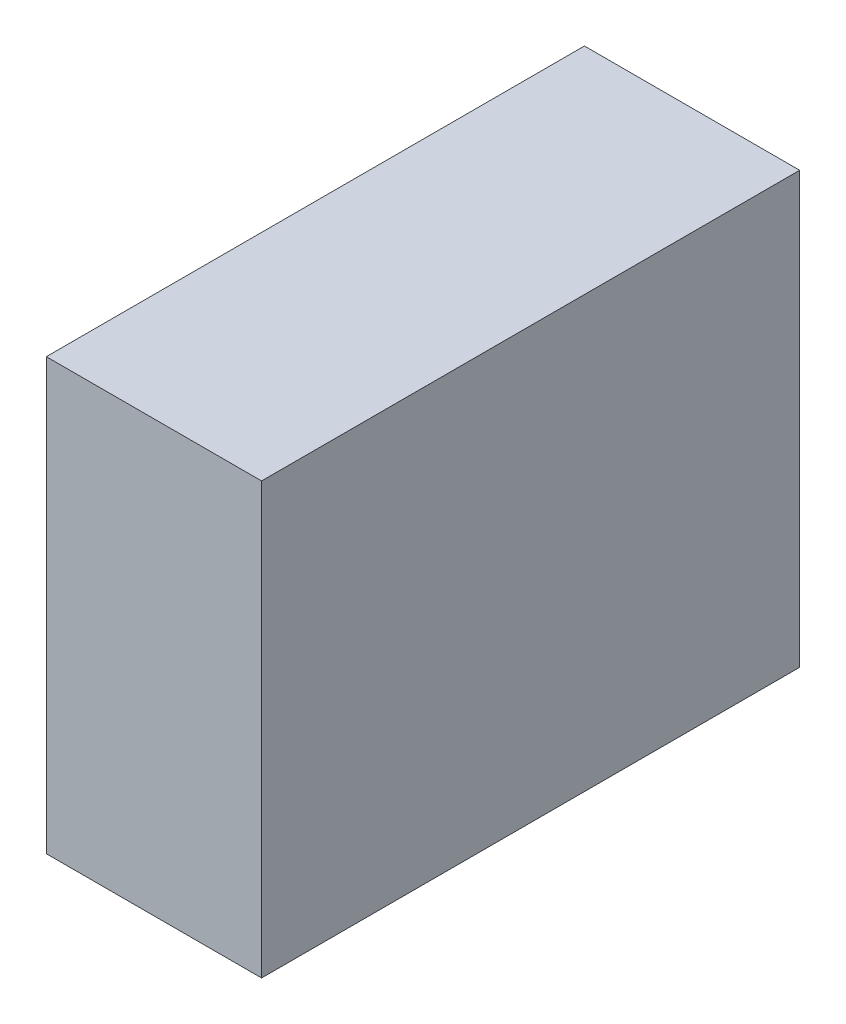
SolidWorks part; units mm, degrees
ref_plane "Front Plane" through (0, 0, 0) normal (0, 0, 1) x (1, 0, 0)
ref_plane "Top Plane" through (0, 0, 0) normal (0, 1, 0) x (1, 0, 0)
ref_plane "Right Plane" through (0, 0, 0) normal (1, 0, 0) x (0, 0, -1)
sketch "Sketch1" plane through (0, 0, 0) normal (1, 0, 0) x (0, 0, -1)
  line L1 (-250, 200) -> (250, 200)
  line L2 (-250, 200) -> (-250, -200)
  line L3 (-250, -200) -> (250, -200)
  line L4 (250, 200) -> (250, -200)
  line L5 (-250, 200) -> (250, -200) construction
  line L6 (-250, -200) -> (250, 200) construction
  point P0 (0, 0)
  dimension "D1" = 500
  dimension "D2" = 400
extrude "Boss-Extrude1" add sketch "Sketch1" along normal blind 200
